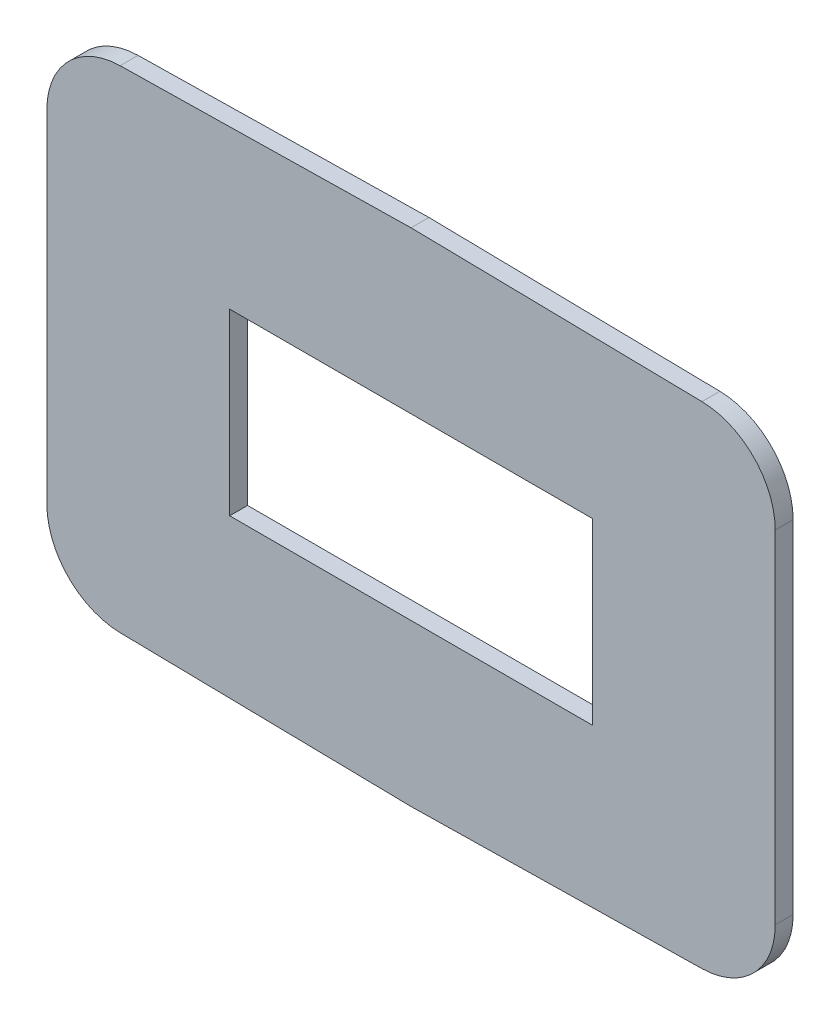
SolidWorks part; units mm, degrees
ref_plane "Front Plane" through (0, 0, 0) normal (0, 0, 1) x (1, 0, 0)
ref_plane "Top Plane" through (0, 0, 0) normal (0, 1, 0) x (1, 0, 0)
ref_plane "Right Plane" through (0, 0, 0) normal (1, 0, 0) x (0, 0, -1)
sketch "Sketch1" plane through (0, 0, 0) normal (0, 0, 1) x (1, 0, 0)
  line L0 (-11.7931, 5.1887) -> (-11.7931, -16.1473) construction
  line L1 (3.7097, 4.9181) -> (-11.7931, 5.1887)
  line L2 (-11.7931, -16.1473) -> (3.7097, -15.8767)
  line L3 (-11.7931, -16.1473) -> (-27.2959, -15.8767)
  line L4 (3.7097, 4.9181) -> (3.7097, -15.8767)
  line L5 (3.7097, -5.4793) -> (-26.7791, -5.4793) construction
  line L6 (-4.0715, -5.4793) -> (-19.5147, -5.4793) construction
  line L7 (-4.0715, -1.6693) -> (-19.5147, -1.6693)
  line L8 (-4.0715, -1.6693) -> (-4.0715, -9.2893)
  line L9 (-4.0715, -9.2893) -> (-19.5147, -9.2893)
  line L10 (-19.5147, -1.6693) -> (-19.5147, -9.2893)
  line L11 (-11.7931, -1.6693) -> (-11.7931, -9.2893) construction
  line L12 (-27.2959, 4.9181) -> (-27.2959, -15.8767)
  line L13 (-27.2959, 4.9181) -> (-11.7931, 5.1887)
  dimension "D1" = 91
  dimension "D2" = 91
  dimension "D3" = 15.4432
  dimension "D4" = 7.62
extrude "Extrude1" add sketch "Sketch1" along normal blind 0.762
fillet "Fillet1" radius 3.175 4 edges at (-27.2959, -15.8767, 0.381) (-27.2959, 4.9181, 0.381) (3.7097, -15.8767, 0.381) (3.7097, 4.9181, 0.381)
ref_plane "Plane1" through (-11.7931, 0, 0) normal (-1, 0, 0) x (0, 0, 1)
ref_plane "Plane2" through (0, -5.4793, 0) normal (0, -1, 0) x (1, 0, 0)
